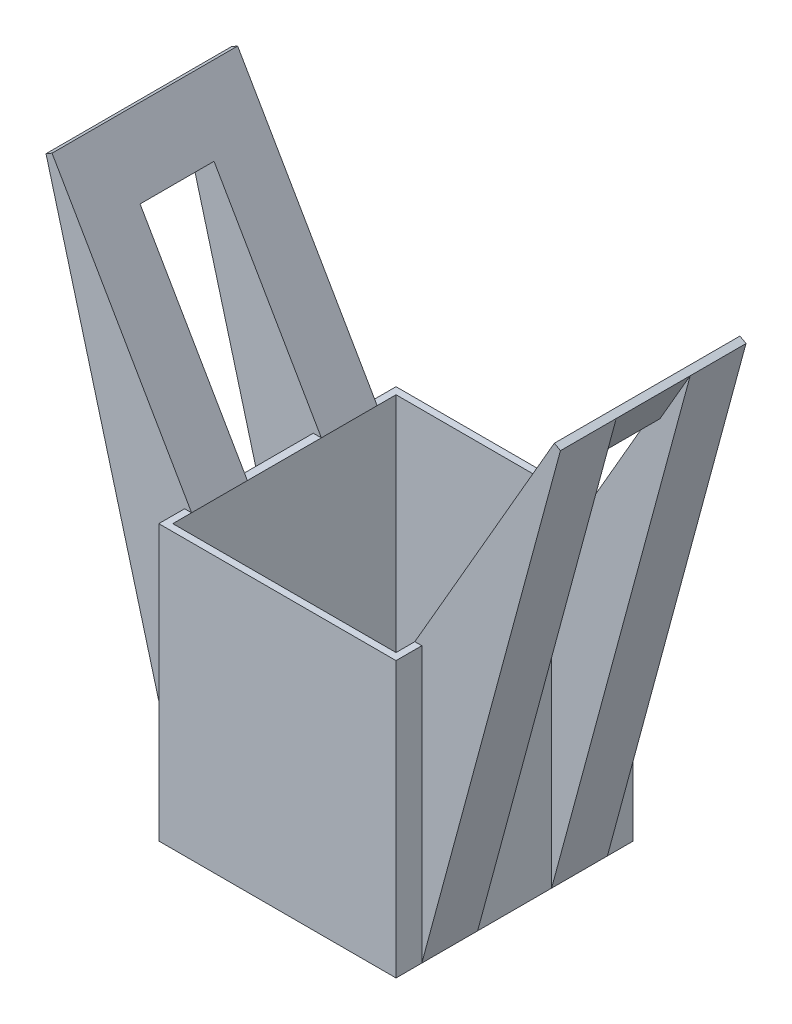
SolidWorks part; units mm, degrees
ref_plane "Ebene vorne" through (0, 0, 0) normal (0, 0, 1) x (1, 0, 0)
ref_plane "Ebene oben" through (0, 0, 0) normal (0, 1, 0) x (1, 0, 0)
ref_plane "Ebene rechts" through (0, 0, 0) normal (1, 0, 0) x (0, 0, -1)
sketch "Skizze1" plane through (0, 0, 0) normal (0, 1, 0) x (1, 0, 0)
  line L0 (-8.5, -8.5) -> (-8.5, 8.5)
  line L1 (8, -8) -> (-8, -8)
  line L2 (8, -8) -> (8, 8)
  line L3 (8, 8) -> (-8, 8)
  line L4 (-8, -8) -> (-8, 8)
  line L5 (8, -8) -> (-8, 8) construction
  line L6 (8, 8) -> (-8, -8) construction
  line L7 (8.5, 8.5) -> (-8.5, 8.5)
  line L8 (8.5, -8.5) -> (8.5, 8.5)
  line L9 (8.5, -8.5) -> (-8.5, -8.5)
  point P0 (0, 0)
  dimension "D1" = 16
  dimension "D2" = 16
  dimension "D3" = 0.5
extrude "Aufsatz-Linear austragen1" add sketch "Skizze1" along normal blind 19.7
ref_plane "Ebene1" through (-2.5304, 1.4609, 0) normal (0.866, -0.5, 0) x (0, 0, -1)
sketch "Skizze10" plane through (-2.5304, 1.4609, 0) normal (0.866, -0.5, 0) x (0, 0, -1)
  line L1 (6.6481, 21.0607) -> (-6.6519, 21.0607)
  line L2 (6.6481, 21.0607) -> (6.6481, 41.0607)
  line L3 (6.6481, 41.0607) -> (-6.6519, 41.0607)
  line L4 (-6.6519, 21.0607) -> (-6.6519, 41.0607)
  line L6 (-8, 21.0607) -> (8, 21.0607) construction
  point P4 (6.65, 21.3107)
  point P5 (6.6481, 21.0607)
  point P6 (-6.65, 21.0607)
  point P7 (0, 0)
  point P9 (0, 0)
  point P11 (-6.6594, 21.3107)
  point P12 (0, 0)
  point P13 (0, 0)
  dimension "D1" = 13.3
  dimension "D2" = 20
  dimension "D3" = 1.3519
extrude "Aufsatz-Linear austragen5" add sketch "Skizze10" along normal blind 0.5
sketch "Skizze11" plane through (8, 0, 0) normal (-1, 0, 0) x (0, 0, 1)
  line L1 (-2.6481, 19.7) -> (2.6519, 19.7)
  line L2 (-2.6481, 19.7) -> (-2.6481, 33.0205)
  line L3 (-2.6481, 33.0205) -> (2.6519, 33.0205)
  line L4 (2.6519, 19.7) -> (2.6519, 33.0205)
  line L5 (-6.6481, 19.7) -> (-6.6481, 37.0205) construction
  line L6 (6.6519, 37.0205) -> (6.6519, 19.7) construction
  line L7 (-6.6481, 37.0205) -> (6.6519, 37.0205) construction
  line L9 (-8.5, 19.7) -> (8.5, 19.7) construction
  point P4 (-2.65, 19.9165)
  point P5 (-2.6481, 19.7)
  point P12 (2.65, 19.7)
  point P13 (0, 0)
  point P15 (0, 0)
  point P16 (0, 0)
  point P17 (0, 0)
  dimension "D1" = 4
  dimension "D2" = 4
  dimension "D3" = 4
extrude "Schnitt-Linear austragen14" cut sketch "Skizze11" against normal through all
sketch "Skizze12" plane through (0, 0, 6.6519) normal (0, 0, 1) x (1, 0, 0)
  line L0 (18.433, 36.7705) -> (8.5, 0)
  line L1 (8.5, 0) -> (8.5, 19.7)
  line L2 (8.5, 19.7) -> (18.433, 36.7705)
  point P4 (0, 0)
extrude "Aufsatz-Linear austragen6" add sketch "Skizze12" against normal up to surface (4 mm away) up to face at (12.134, 26.3603, 2.6519)
sketch "Skizze13" plane through (0, 0, -6.6481) normal (0, 0, -1) x (-1, 0, 0)
  line L0 (-18.433, 36.7705) -> (-8.5, 19.7)
  line L1 (-8.5, 19.7) -> (-8.5, 0)
  line L2 (-8.5, 0) -> (-18.433, 36.7705)
extrude "Aufsatz-Linear austragen7" add sketch "Skizze13" against normal up to surface (4 mm away) up to face at (12.134, 26.3603, -2.6481)
mirror "Spiegeln6" about plane through (0, 0, 0) normal (1, 0, 0) of "Aufsatz-Linear austragen7", "Aufsatz-Linear austragen6", "Schnitt-Linear austragen14", "Aufsatz-Linear austragen5"
